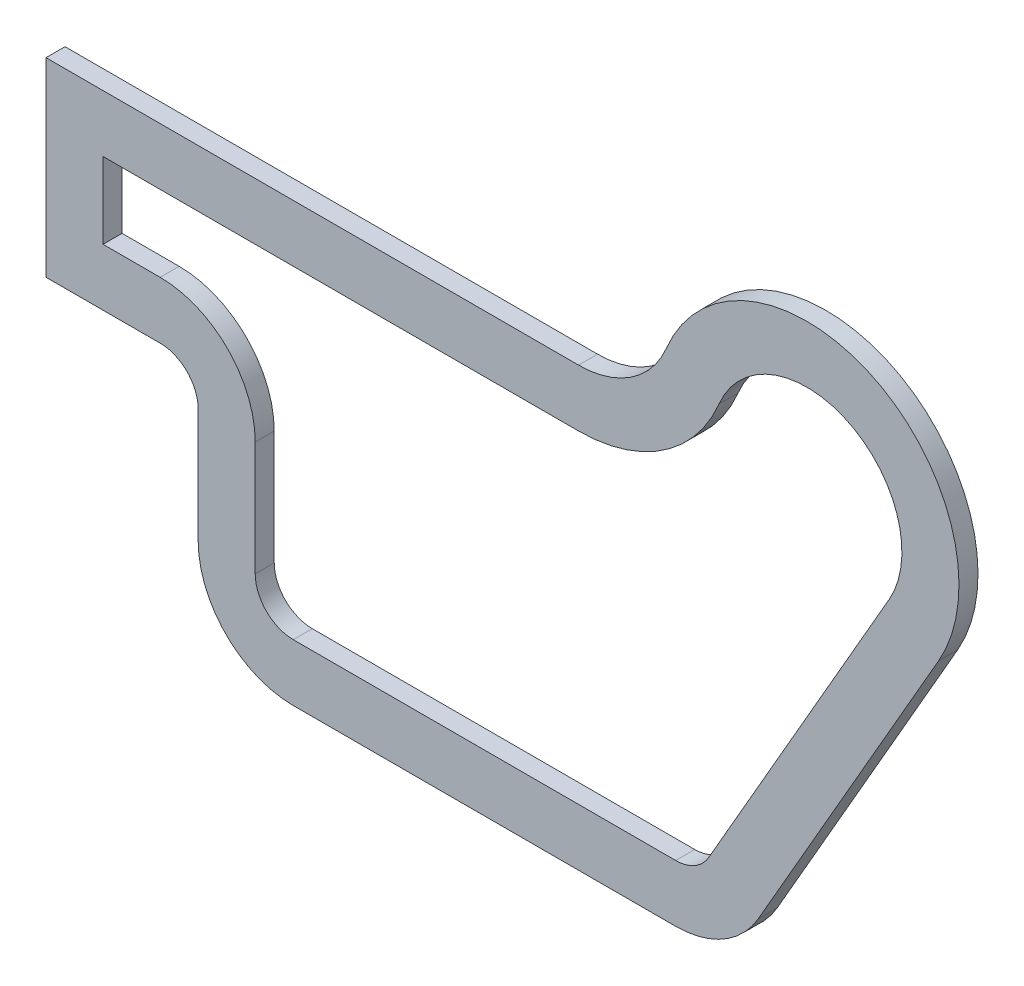
SolidWorks part; units mm, degrees
ref_plane "Front Plane" through (0, 0, 0) normal (0, 0, 1) x (1, 0, 0)
ref_plane "Top Plane" through (0, 0, 0) normal (0, 1, 0) x (1, 0, 0)
ref_plane "Right Plane" through (0, 0, 0) normal (1, 0, 0) x (0, 0, -1)
sketch "Sketch1" plane through (0, 0, 0) normal (0, 0, 1) x (1, 0, 0)
  line L0 (140, 181.336) -> (0, 181.336)
  line L1 (0, 181.336) -> (0, 131.336)
  line L2 (0, 131.336) -> (30, 131.336)
  line L3 (40, 121.336) -> (40, 91.336)
  line L4 (65, 66.336) -> (165.5389, 66.336)
  line L5 (187.21, 78.8714) -> (234.6737, 161.3927)
  arc A0 (234.6737, 161.3927) -> (163.0769, 196.7206) centre (200, 181.336) ccw
  arc A1 (40, 91.336) -> (65, 66.336) centre (65, 91.336) ccw
  arc A2 (165.5389, 66.336) -> (187.21, 78.8714) centre (165.5389, 91.336) ccw
  arc A3 (163.0769, 196.7206) -> (140, 181.336) centre (140, 206.336) cw
  arc A4 (40, 121.336) -> (30, 131.336) centre (30, 121.336) ccw
  point P4 (234.7756, 162.0075)
  point P14 (180, 66.336)
  point P17 (160, 181.336)
  dimension "D1" = 50
  dimension "D3" = 80
  dimension "D7" = 25
  dimension "D8" = 10
  dimension "D2" = 115
  dimension "D4" = 40
  dimension "D5" = 180
  dimension "D6" = 200
extrude "Boss-Extrude1" add sketch "Sketch1" along normal blind 5
shell "Shell1" thickness 15
